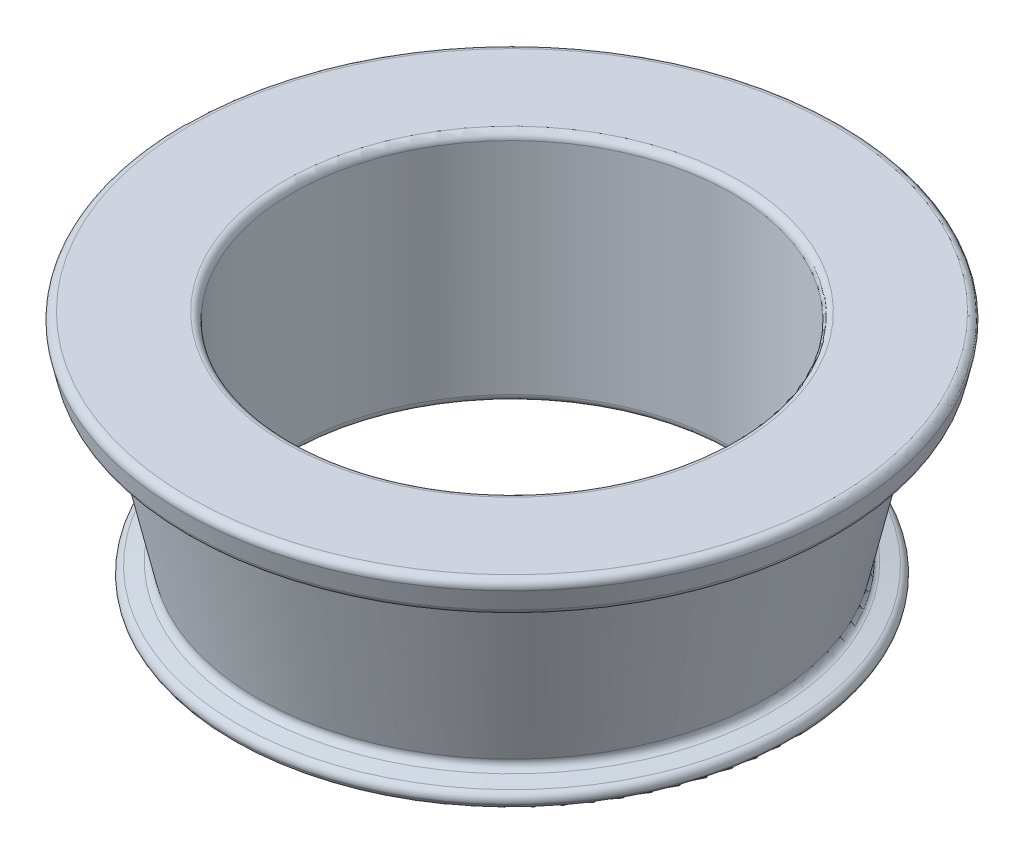
SolidWorks part; units mm, degrees
ref_plane "Front Plane" through (0, 0, 0) normal (0, 0, 1) x (1, 0, 0)
ref_plane "Top Plane" through (0, 0, 0) normal (0, 1, 0) x (1, 0, 0)
ref_plane "Right Plane" through (0, 0, 0) normal (1, 0, 0) x (0, 0, -1)
sketch "Sketch1" plane through (0, 0, 0) normal (0, 0, 1) x (1, 0, 0)
  line L0 (0, 0) -> (-22.5619, 0) construction
  line L1 (0, 0) -> (0, 21.6074) construction
  line L2 (-15, 0) -> (-15, 16)
  line L3 (-15, 16) -> (-22.6, 16)
  line L4 (-22.6, 16) -> (-22.0504, 13.5612)
  line L5 (-22.0504, 13.5612) -> (-20.0993, 14.0009)
  line L6 (-20.0993, 14.0009) -> (-17.2485, 1.3507)
  line L7 (-17.2485, 1.3507) -> (-19.2485, 0.9)
  line L8 (-19.2485, 0.9) -> (-19, 0)
  line L9 (-19, 0) -> (-15, 0)
  dimension "D1" = 15
  dimension "D2" = 16
  dimension "D3" = 4
  dimension "D4" = 0.9
  dimension "D5" = 7.6
  dimension "D6" = 77.3
  dimension "D7" = 2
  dimension "D8" = 2
  dimension "D9" = 2.5
revolve "Revolve1" add sketch "Sketch1" angle 360 about L1
fillet "Fillet1" radius 0.5 2 edges at (0, 0, -15) (0, 16, -15)
fillet "Fillet2" radius 0.5 6 edges at (0, 0, -19) (0, 16, -22.6) (0, 0.9, -19.2485) (0, 1.3507, -17.2485) (0, 14.0009, -20.0993) (0, 13.5612, -22.0504)
